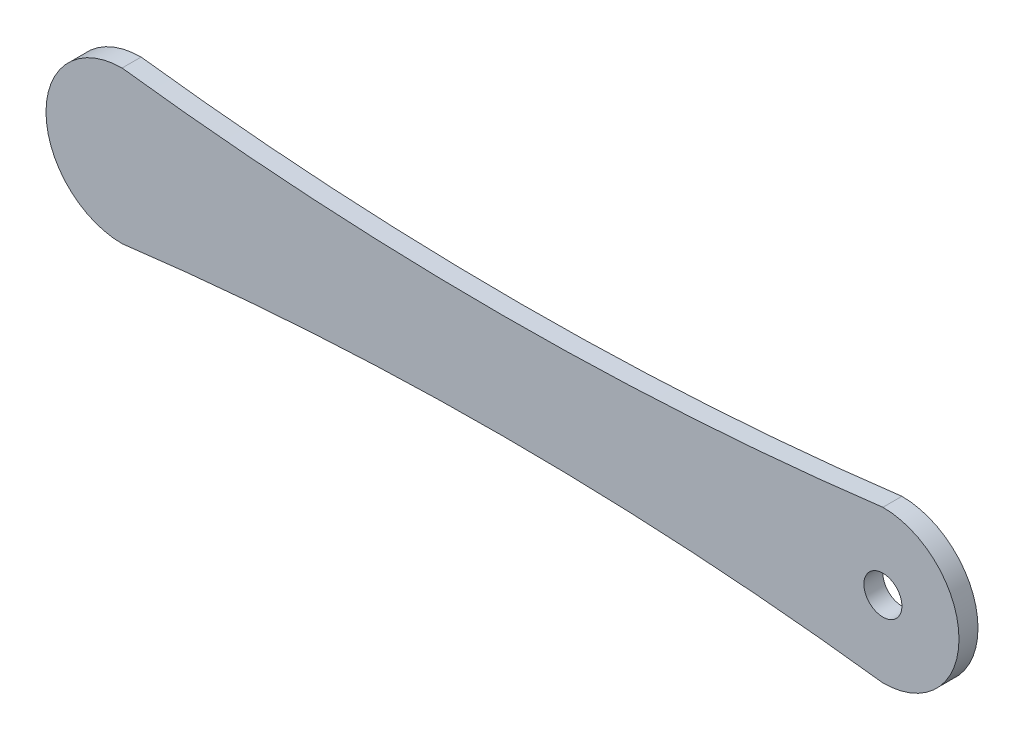
SolidWorks part; units mm, degrees
ref_plane "Front Plane" through (0, 0, 0) normal (0, 0, 1) x (1, 0, 0)
ref_plane "Top Plane" through (0, 0, 0) normal (0, 1, 0) x (1, 0, 0)
ref_plane "Right Plane" through (0, 0, 0) normal (1, 0, 0) x (0, 0, -1)
sketch "Sketch1" plane through (0, 0, 0) normal (0, 0, 1) x (1, 0, 0)
  line L0 (-500, 0) -> (500, 0) construction
  line L1 (-500, -100) -> (500, -100) construction
  line L3 (-500, 100) -> (500, 100) construction
  line L5 (-500, -100) -> (500, 100) construction
  line L6 (-500, 100) -> (500, -100) construction
  arc A0 (-500, 100) -> (-500, -100) centre (-500, 0) ccw
  arc A1 (500, -100) -> (500, 100) centre (500, 0) ccw
  arc A2 (-500, 100) -> (500, 100) centre (0, 4068.627) ccw
  arc A3 (-500, -100) -> (500, -100) centre (0, -4068.627) cw
  point P0 (0, 0)
  dimension "D6" = 4000
  dimension "D2" = 100
  dimension "D1" = 1000
  dimension "D3" = 200
extrude "Boss-Extrude1" add sketch "Sketch1" along normal blind 25
sketch "Sketch2" plane through (0, 0, 0) normal (0, 0, -1) x (1, 0, 0)
  circle A0 centre (-500, 0) radius 50
  dimension "D2" = 500
  dimension "D1" = 100
extrude "Boss-Extrude2" add sketch "Sketch2" along normal blind 25
sketch "Sketch3" plane through (0, 0, 25) normal (0, 0, 1) x (1, 0, 0)
  circle A1 centre (500, 0) radius 25
  dimension "D2" = 50
  dimension "D1" = 500
extrude "Cut-Extrude2" cut sketch "Sketch3" against normal blind 25
